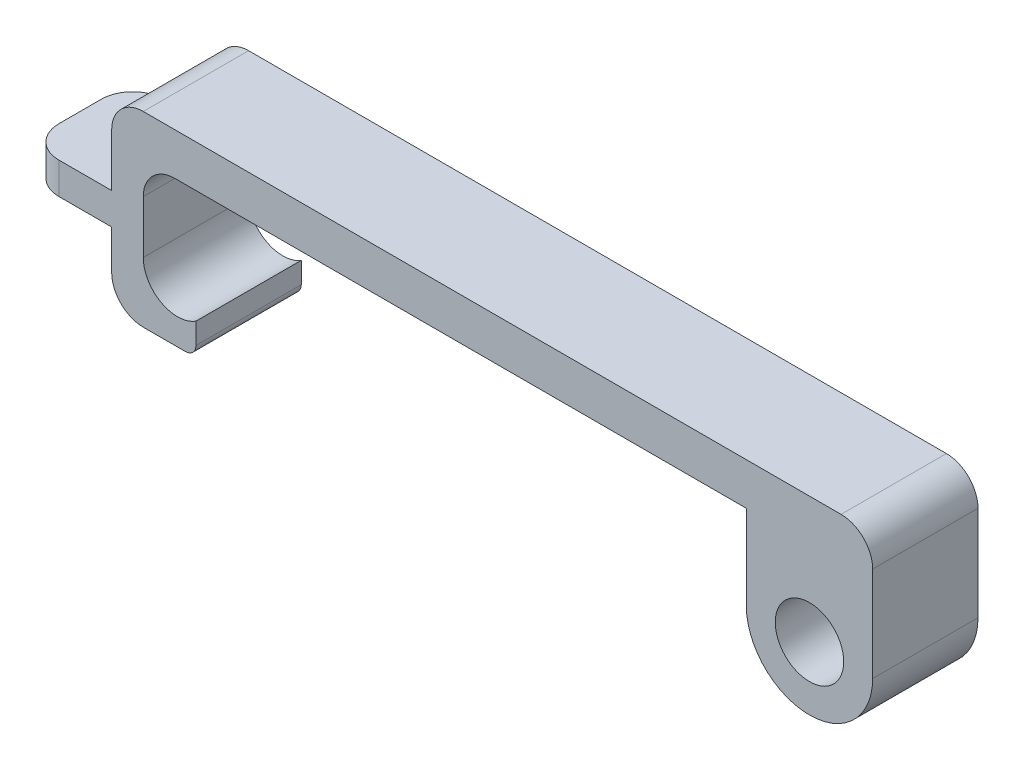
SolidWorks part; units mm, degrees
ref_plane "Plan de face" through (0, 0, 0) normal (0, 0, 1) x (1, 0, 0)
ref_plane "Plan de dessus" through (0, 0, 0) normal (0, 1, 0) x (1, 0, 0)
ref_plane "Plan de droite" through (0, 0, 0) normal (1, 0, 0) x (0, 0, -1)
sketch "Esquisse1" plane through (0, 0, 0) normal (0, 0, 1) x (1, 0, 0)
  line L0 (11.5884, 24.9102) -> (11.5884, -49.0898) construction
  line L1 (11.5884, 18.9102) -> (11.5884, 26.9102)
  line L2 (11.5884, 25.9102) -> (-36.4116, 25.9102) construction
  line L3 (11.5884, 26.9102) -> (-45.6616, 26.9102)
  line L4 (-45.6616, 26.9102) -> (-45.6616, 18.9102)
  line L5 (-48.6616, 22.9102) -> (-48.6616, 30.9102)
  line L6 (-40.6616, 16.1716) -> (-40.6616, 13.1716)
  line L7 (-40.6616, 13.1716) -> (-48.6616, 13.1716)
  line L8 (-48.6616, 13.1716) -> (-48.6616, 19.9102)
  line L9 (-48.6616, 30.9102) -> (23.5884, 30.9102)
  line L10 (23.5884, 30.9102) -> (23.5884, 18.9102)
  line L11 (-48.6616, 22.9102) -> (-56.6616, 22.9102)
  line L13 (-48.6616, 19.9102) -> (-56.6616, 19.9102)
  line L14 (-56.6616, 22.9102) -> (-56.6616, 19.9102)
  circle A0 centre (17.5884, 18.9102) radius 3.25
  arc A1 (11.5884, 18.9102) -> (23.5884, 18.9102) centre (17.5884, 18.9102) ccw
  circle A2 centre (-42.4116, 18.9102) radius 3.25 construction
  arc A3 (-45.6616, 18.9102) -> (-40.6616, 16.1716) centre (-42.4116, 18.9102) ccw
  dimension "D1" = 6.5
  dimension "D2" = 1
  dimension "D3" = 8
  dimension "D4" = 4
  dimension "D5" = 3
  dimension "D6" = 3
  dimension "D7" = 8
  dimension "D8" = 8
  dimension "D9" = 3
extrude "Boss.-Extru.1" add sketch "Esquisse1" along normal blind 10
fillet "Congé1" radius 3 6 edges at (-45.6616, 26.9102, 5) (-48.6616, 13.1716, 5) (23.5884, 30.9102, 5) (-48.6616, 30.9102, 5) (-56.6616, 21.4102, 10) (-56.6616, 21.4102, 0)
fillet "Congé2" radius 1 1 edges at (-40.6616, 13.1716, 5)
